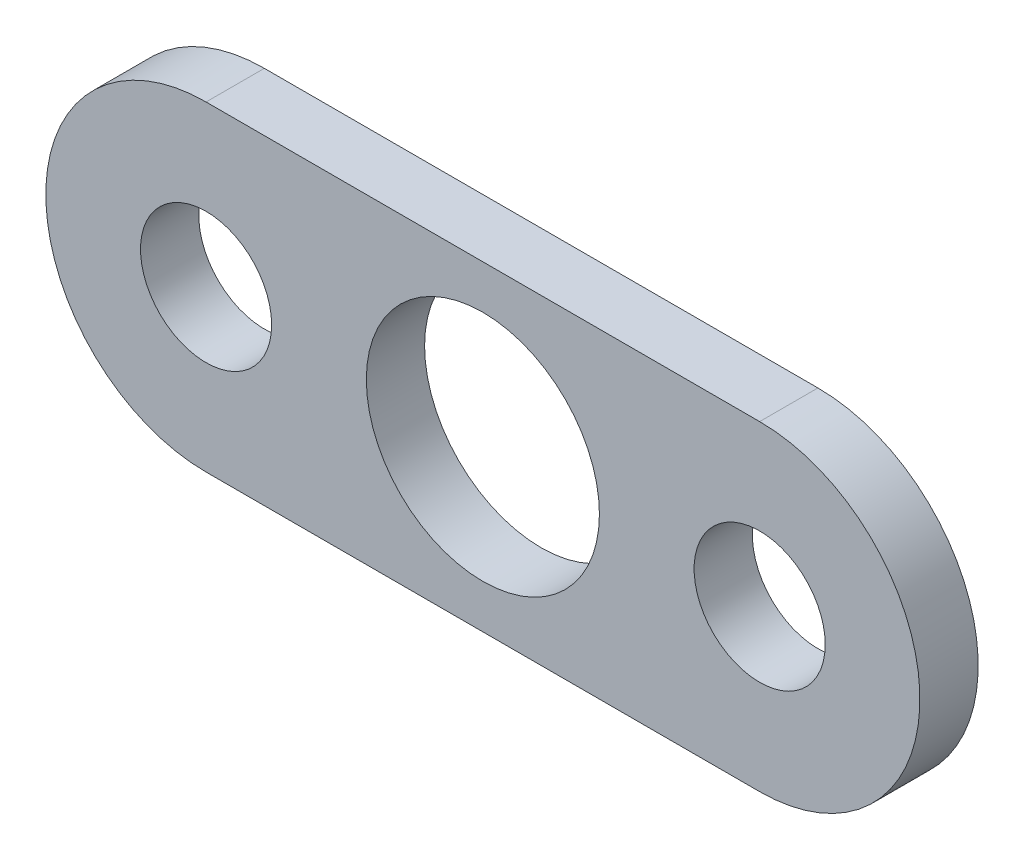
SolidWorks part; units mm, degrees
material "3.3315 (EN-AW 5005)"
ref_plane "Front Plane" through (0, 0, 0) normal (0, 0, 1) x (1, 0, 0)
ref_plane "Top Plane" through (0, 0, 0) normal (0, 1, 0) x (1, 0, 0)
ref_plane "Right Plane" through (0, 0, 0) normal (1, 0, 0) x (0, 0, -1)
sketch "Sketch1" plane through (0, 0, 0) normal (0, 0, 1) x (1, 0, 0)
  line L0 (-9.5, 0) -> (9.5, 0) construction
  line L1 (-9.5, 5.5) -> (9.5, 5.5)
  line L2 (-9.5, -5.5) -> (9.5, -5.5)
  circle A0 centre (0, 0) radius 4
  arc A1 (-9.5, 5.5) -> (-9.5, -5.5) centre (-9.5, 0) ccw
  arc A2 (9.5, -5.5) -> (9.5, 5.5) centre (9.5, 0) ccw
  point P5 (0, 0)
  dimension "D1" = 8
  dimension "D2" = 11
  dimension "D3" = 19
extrude "Boss-Extrude1" add sketch "Sketch1" along normal blind 2
hole_wizard "M4 Clearance Hole1" positions "Sketch2" profile "Sketch3" hole size "M4" standard "ISO" end condition through all
sketch "Sketch2" plane through (0, 0, 2) normal (0, 0, 1) x (1, 0, 0)
  point P0 (-9.5, 0)
  point P3 (9.5, 0)
sketch "Sketch3" plane through (-9.5, 0, 2) normal (1, 0, 0) x (0, -1, 0)
  line L0 (0, 0) -> (0, 2)
  line L1 (0, 2) -> (2.25, 2)
  line L2 (2.25, 2) -> (2.25, 0)
  line L5 (2.25, 0) -> (0, 0)
  line L11 (0, -6.35) -> (0, 107.95) construction
  dimension "Thru Hole Dia." = 4.5
  dimension "Thru Hole Depth" = 2
